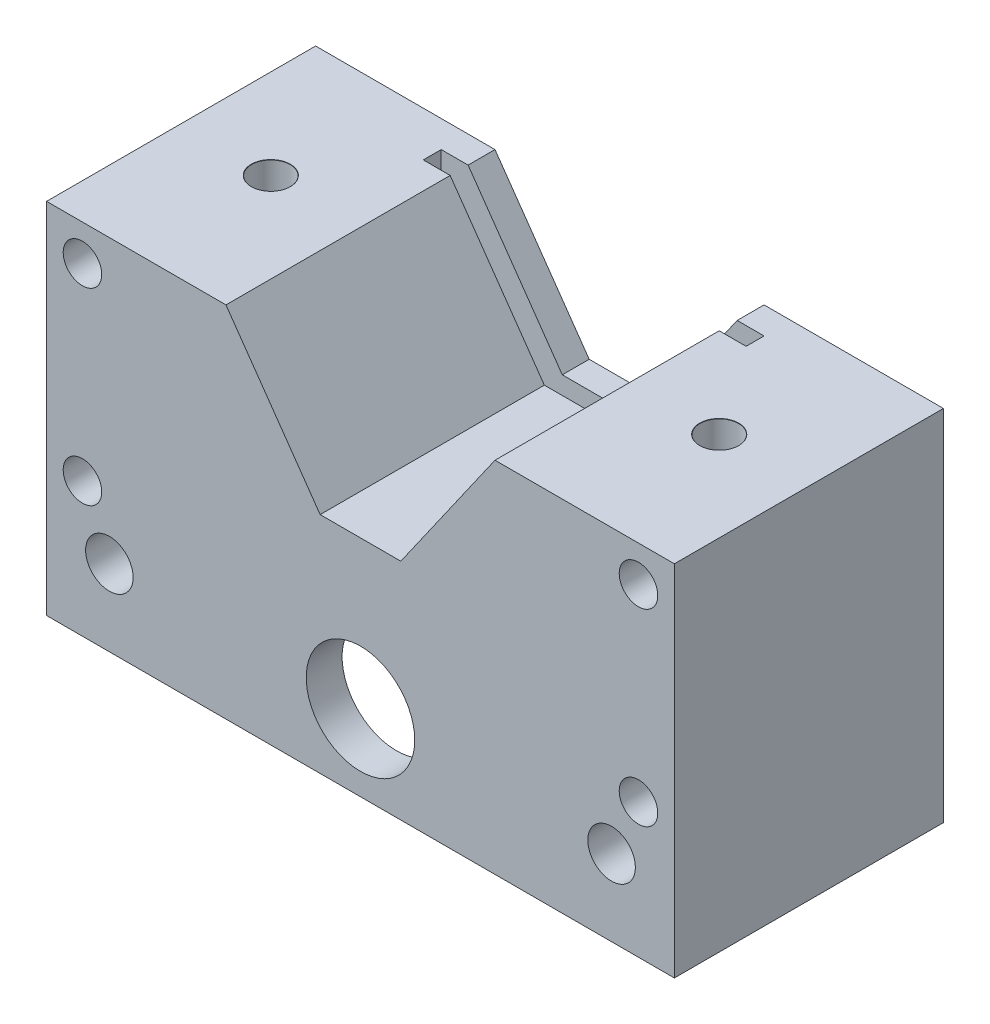
SolidWorks part; units mm, degrees
ref_plane "Ebene vorne" through (0, 0, 0) normal (0, 0, 1) x (1, 0, 0)
ref_plane "Ebene oben" through (0, 0, 0) normal (0, 1, 0) x (1, 0, 0)
ref_plane "Ebene rechts" through (0, 0, 0) normal (1, 0, 0) x (0, 0, -1)
sketch "Skizze1" plane through (0, 0, 0) normal (0, 0, 1) x (1, 0, 0)
  line L0 (26.4288, -31.3727) -> (-43.5712, -31.3727)
  line L1 (-43.5712, -31.3727) -> (-43.5712, 8.6273)
  line L2 (26.4288, -31.3727) -> (26.4288, 8.6273)
  line L3 (26.4288, 8.6273) -> (6.4288, 8.6273)
  line L4 (6.4288, 8.6273) -> (-4.0743, -6.3727)
  line L5 (-13.068, -6.3727) -> (-4.0743, -6.3727)
  line L6 (-13.068, -6.3727) -> (-23.5712, 8.6273)
  line L7 (-23.5712, 8.6273) -> (-43.5712, 8.6273)
  dimension "D1" = 40
  dimension "D2" = 70
  dimension "D3" = 40
  dimension "D4" = 20
  dimension "D5" = 20
  dimension "D6" = 25
  dimension "D7" = 235
  dimension "D8" = 235
extrude "Aufsatz-Linear austragen1" add sketch "Skizze1" along normal blind 30
hole_wizard "Durchgangsloch für M51" positions "Skizze2" profile "Skizze3" hole size "M5" standard "ISO" end condition through all
sketch "Skizze2" plane through (0, 0, 30) normal (0, 0, 1) x (1, 0, 0)
  line L0 (-43.5712, 8.6273) -> (-43.5712, -31.3727) construction
  line L1 (-43.5712, -31.3727) -> (26.4288, -31.3727) construction
  line L2 (26.4288, -31.3727) -> (26.4288, 8.6273) construction
  point P0 (-36.5712, -22.8727)
  point P2 (19.4288, -22.8727)
  dimension "D1" = 7
  dimension "D2" = 8.5
  dimension "D3" = 7
  dimension "D4" = 8.5
sketch "Skizze3" plane through (-36.5712, -22.8727, 30) normal (1, 0, 0) x (0, -1, 0)
  line L0 (0, 0) -> (0, 30)
  line L1 (0, 30) -> (2.65, 30)
  line L2 (2.65, 30) -> (2.65, 0)
  line L5 (2.65, 0) -> (0, 0)
  line L11 (0, -6.35) -> (0, 107.95) construction
  dimension "Bohrerdurchmesser" = 5.3
  dimension "Bohrungstiefe" = 30
hole_wizard "Durchgangsloch für M43" positions "Skizze4" profile "Skizze5" hole size "M4" standard "ISO"
sketch "Skizze4" plane through (0, -31.3727, 0) normal (0, -1, 0) x (-1, 0, 0)
  line L0 (-26.4288, -30) -> (-26.4288, 0) construction
  line L1 (43.5712, -30) -> (43.5712, 0) construction
  line L2 (43.5712, -30) -> (-26.4288, -30) construction
  point P0 (36.5712, -15)
  point P2 (-19.4288, -15)
  dimension "D1" = 7
  dimension "D2" = 7
  dimension "D3" = 15
  dimension "D4" = 15
sketch "Skizze5" plane through (-36.5712, -31.3727, 15) normal (1, 0, 0) x (0, 0, -1)
  line L0 (0, 0) -> (0, 5.85)
  line L1 (0, 5.85) -> (2.15, 5.85)
  line L2 (2.15, 5.85) -> (2.15, 0)
  line L5 (2.15, 0) -> (0, 0)
  line L11 (0, -6.35) -> (0, 107.95) construction
  dimension "Bohrerdurchmesser" = 4.3
  dimension "Bohrungstiefe" = 5.85
hole_wizard "Durchgangsloch für M41" positions "Skizze19" profile "Skizze20" hole size "M4" standard "ISO" end condition through all
sketch "Skizze19" plane through (0, 0, 0) normal (0, 0, -1) x (-1, 0, 0)
  line L0 (-26.4288, -31.3727) -> (-26.4288, 8.6273) construction
  line L1 (43.5712, 8.6273) -> (43.5712, -31.3727) construction
  line L2 (23.5712, 8.6273) -> (43.5712, 8.6273) construction
  line L3 (-26.4288, 8.6273) -> (-6.4288, 8.6273) construction
  point P0 (-22.4288, 4.6273)
  point P2 (-22.4288, -16.3727)
  point P4 (39.5712, -16.3727)
  point P6 (39.5712, 4.6273)
  dimension "D1" = 4
  dimension "D2" = 4
  dimension "D3" = 4
  dimension "D4" = 4
  dimension "D5" = 4
  dimension "D6" = 4
  dimension "D7" = 21
  dimension "D8" = 21
sketch "Skizze20" plane through (22.4288, 4.6273, 0) normal (1, 0, 0) x (0, 1, 0)
  line L0 (0, 0) -> (0, 30)
  line L1 (0, 30) -> (2.15, 30)
  line L2 (2.15, 30) -> (2.15, 0.025)
  line L3 (2.15, 0.025) -> (2.175, 0)
  line L5 (2.175, 0) -> (0, 0)
  line L6 (-2.15, 0.025) -> (-2.175, 0) construction
  line L11 (0, -6.35) -> (0, 107.95) construction
  dimension "Bohrerdurchmesser" = 4.3
  dimension "Bohrungstiefe" = 30
  dimension "Senkdurchmesser2 (Oben)" = 4.35
  dimension "Senkwinkel2 (Oben)" = 90
sketch "Skizze21" plane through (0, -31.3727, 0) normal (0, -1, 0) x (1, 0, 0)
  line L0 (-43.5712, 30) -> (-43.5712, 0) construction
  line L1 (-28.5712, 6) -> (11.4288, 6)
  line L2 (-28.5712, 6) -> (-28.5712, 26)
  line L3 (-28.5712, 26) -> (11.4288, 26)
  line L4 (11.4288, 6) -> (11.4288, 26)
  line L5 (-8.5712, 26) -> (-8.5712, 6) construction
  line L6 (-28.5712, 16) -> (11.4288, 16) construction
  line L7 (26.4288, 30) -> (26.4288, 0) construction
  line L8 (-43.5712, 0) -> (26.4288, 0) construction
  line L9 (-43.5712, 30) -> (26.4288, 30) construction
  point P0 (-8.5712, 16)
  dimension "D1" = 15
  dimension "D2" = 15
  dimension "D3" = 40
  dimension "D4" = 6
  dimension "D5" = 4
  dimension "D6" = 20
extrude "Schnitt-Linear austragen5" cut sketch "Skizze21" against normal blind 22
sketch "Skizze22" plane through (0, 0, 0) normal (0, 0, -1) x (-1, 0, 0)
  line L0 (43.5712, 8.6273) -> (43.5712, -31.3727) construction
  line L1 (43.5712, -31.3727) -> (-26.4288, -31.3727) construction
  circle A0 centre (8.5712, -22.8727) radius 6.05
  dimension "D1" = 35
  dimension "D2" = 8.5
extrude "Schnitt-Linear austragen6" cut sketch "Skizze22" against normal blind 4.5
hole_wizard "Ø6.2 (6.2) Durchmesser Bohrung1" positions "Skizze23" profile "Skizze24" hole size "Ø6.2" standard "ISO" end condition through all
sketch "Skizze23" plane through (0, 0, 4.5) normal (0, 0, -1) x (-1, 0, 0)
  line L0 (43.5712, 8.6273) -> (43.5712, -31.3727) construction
  line L1 (43.5712, -31.3727) -> (-26.4288, -31.3727) construction
  point P0 (8.5712, -22.8727)
  dimension "D1" = 35
  dimension "D2" = 8.5
sketch "Skizze24" plane through (-8.5712, -22.8727, 4.5) normal (1, 0, 0) x (0, 1, 0)
  line L0 (0, 0) -> (0, 25.5)
  line L1 (0, 25.5) -> (3.1, 25.5)
  line L2 (3.1, 25.5) -> (3.1, 0.025)
  line L3 (3.1, 0.025) -> (3.125, 0)
  line L5 (3.125, 0) -> (0, 0)
  line L6 (-3.1, 0.025) -> (-3.125, 0) construction
  line L11 (0, -6.35) -> (0, 107.95) construction
  dimension "Bohrerdurchmesser" = 6.2
  dimension "Bohrungstiefe" = 25.5
  dimension "Senkdurchmesser2 (Oben)" = 6.25
  dimension "Senkwinkel2 (Oben)" = 90
sketch "Skizze25" plane through (0, 0, 30) normal (0, 0, 1) x (1, 0, 0)
  line L0 (26.4288, -31.3727) -> (26.4288, 8.6273) construction
  line L1 (-43.5712, -31.3727) -> (26.4288, -31.3727) construction
  circle A0 centre (-8.5712, -22.8727) radius 6.05
  dimension "D1" = 35
  dimension "D2" = 8.5
extrude "Schnitt-Linear austragen7" cut sketch "Skizze25" against normal blind 4
sketch "Skizze28" plane through (0, 8.6273, 0) normal (0, 1, 0) x (1, 0, 0)
  line L0 (-43.5712, -30) -> (-43.5712, 0) construction
  line L1 (-23.5712, -30) -> (-43.5712, -30) construction
  line L2 (26.4288, -30) -> (6.4288, -30) construction
  line L3 (26.4288, -30) -> (26.4288, 0) construction
  point P0 (-33.5712, -15)
  point P2 (16.4288, -15)
  dimension "D1" = 10
  dimension "D2" = 15
  dimension "D3" = 15
  dimension "D4" = 10
hole_wizard "Durchgangsloch für M42" positions "Skizze28" profile "Skizze27" hole size "M4" standard "ISO"
sketch "Skizze27" plane through (-33.5712, 8.6273, 15) normal (1, 0, 0) x (0, 0, 1)
  line L0 (0, 0) -> (0, 10.2919)
  line L1 (0, 10.2919) -> (2.15, 9)
  line L2 (2.15, 9) -> (2.15, 0.025)
  line L3 (2.15, 0.025) -> (2.175, 0)
  line L5 (2.175, 0) -> (0, 0)
  line L6 (-2.15, 0.025) -> (-2.175, 0) construction
  line L10 (0, 10.2919) -> (-2.15, 9) construction
  line L11 (0, -6.35) -> (0, 107.95) construction
  dimension "Bohrerdurchmesser" = 4.3
  dimension "Bohrungstiefe" = 9
  dimension "Senkdurchmesser2 (Oben)" = 4.35
  dimension "Senkwinkel2 (Oben)" = 90
  dimension "Spitzenwinkel" = 118
sketch "Skizze30" plane through (0, 8.6273, 0) normal (0, 1, 0) x (1, 0, 0)
  line L0 (-43.5712, -30) -> (-43.5712, 0) construction
  line L1 (9.4288, -5) -> (-26.5712, -5)
  line L2 (9.4288, -5) -> (9.4288, -3)
  line L3 (9.4288, -3) -> (-26.5712, -3)
  line L4 (-26.5712, -5) -> (-26.5712, -3)
  line L6 (26.4288, -30) -> (26.4288, 0) construction
  line L7 (-23.5712, 0) -> (-43.5712, 0) construction
  dimension "D1" = 17
  dimension "D2" = 17
  dimension "D3" = 3
  dimension "D4" = 2
extrude "Schnitt-Linear austragen8" cut sketch "Skizze30" against normal blind 23
